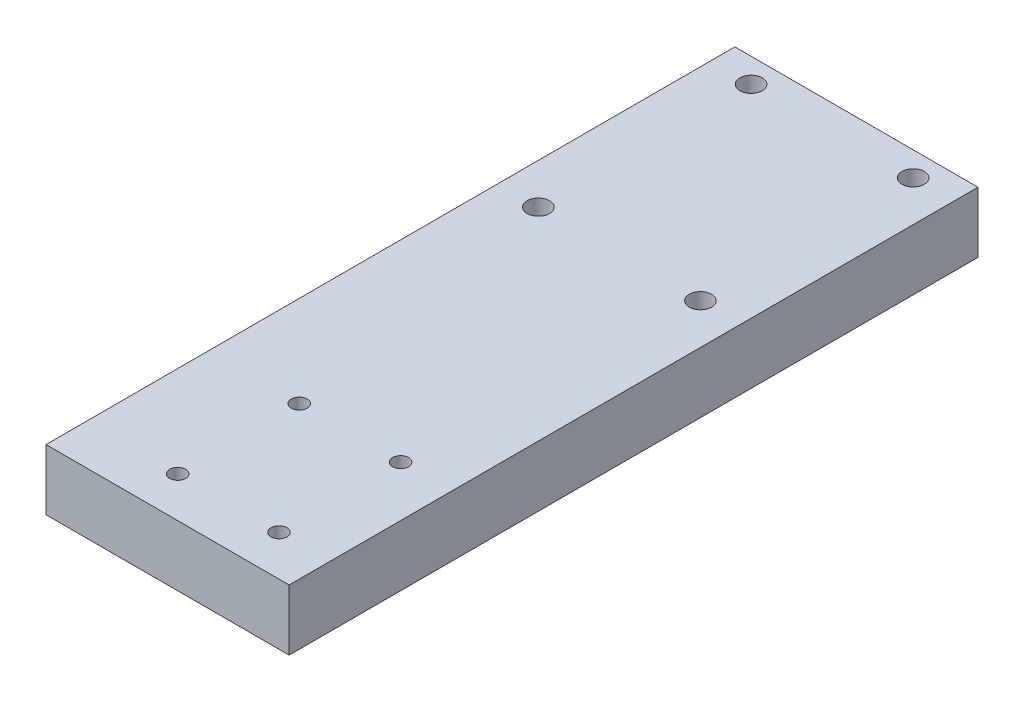
SolidWorks part; units mm, degrees
ref_plane "Front Plane" through (0, 0, 0) normal (0, 0, 1) x (1, 0, 0)
ref_plane "Top Plane" through (0, 0, 0) normal (0, 1, 0) x (1, 0, 0)
ref_plane "Right Plane" through (0, 0, 0) normal (1, 0, 0) x (0, 0, -1)
sketch "Sketch2" plane through (0, 0, 0) normal (0, 0, 1) x (1, 0, 0)
  line L1 (0, 0) -> (76.2, 0)
  line L2 (0, 0) -> (0, 19.05)
  line L3 (0, 19.05) -> (76.2, 19.05)
  line L4 (76.2, 0) -> (76.2, 19.05)
  dimension "D1" = 19.05
  dimension "D2" = 76.2
extrude "Boss-Extrude1" add sketch "Sketch2" along normal blind 215.9
sketch "Sketch3" plane through (0, 19.05, 0) normal (0, 1, 0) x (1, 0, 0)
  line L0 (76.2, 0) -> (0, 0) construction
  line L1 (0, -215.9) -> (0, 0) construction
  circle A0 centre (12.7, -7.62) radius 3.5
  circle A1 centre (63.5, -7.62) radius 3.5
  circle A2 centre (63.5, -74.295) radius 3.5
  circle A3 centre (12.7, -74.295) radius 3.5
  dimension "D1" = 7.62
  dimension "D2" = 12.7
  dimension "D3" = 2
  dimension "D4" = 2
extrude "Cut-Extrude1" cut sketch "Sketch3" against normal through all
sketch "Sketch4" plane through (0, 19.05, 0) normal (0, 1, 0) x (1, 0, 0)
  line L0 (76.2, -215.9) -> (0, -215.9) construction
  line L1 (0, -215.9) -> (0, 0) construction
  circle A0 centre (28.575, -203.2) radius 2.5
  circle A1 centre (60.325, -203.2) radius 2.5
  circle A2 centre (60.325, -165.1) radius 2.5
  circle A3 centre (28.575, -165.1) radius 2.5
  dimension "D1" = 12.7
  dimension "D2" = 28.575
  dimension "D3" = 2
  dimension "D4" = 2
extrude "Cut-Extrude2" cut sketch "Sketch4" against normal through all
